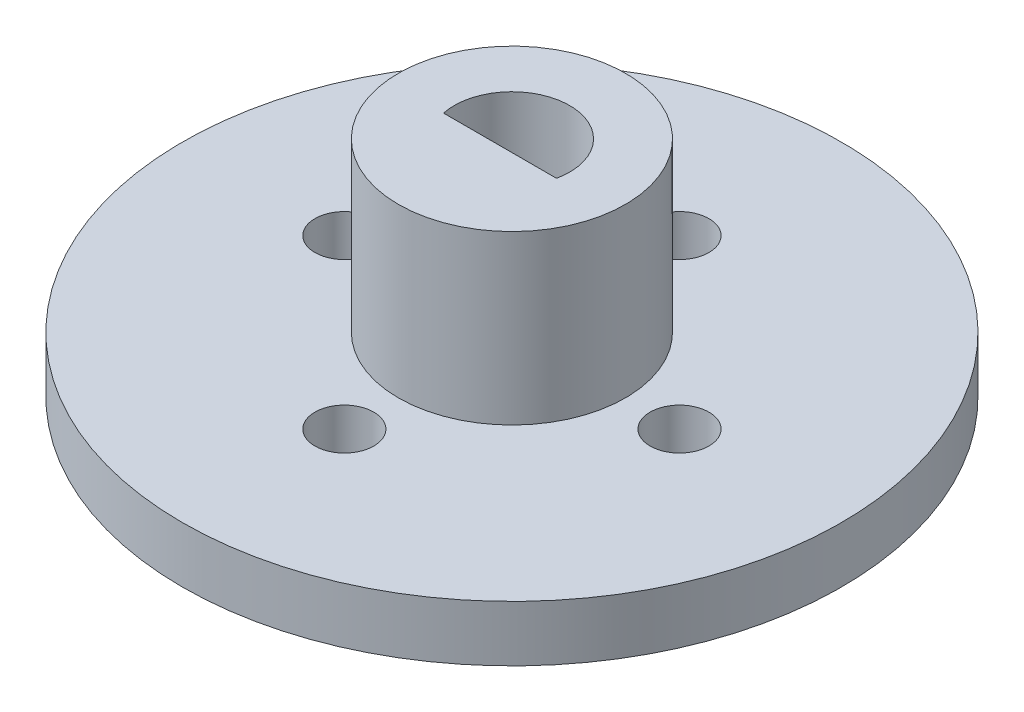
SolidWorks part; units mm, degrees
ref_plane "Front Plane" through (0, 0, 0) normal (0, 0, 1) x (1, 0, 0)
ref_plane "Top Plane" through (0, 0, 0) normal (0, 1, 0) x (1, 0, 0)
ref_plane "Right Plane" through (0, 0, 0) normal (1, 0, 0) x (0, 0, -1)
sketch "Sketch2" plane through (0, 0, 0) normal (0, 1, 0) x (-1, 0, 0)
  circle A0 centre (0, 0) radius 17.7
  dimension "D1" = 35.4
extrude "Boss-Extrude3" add sketch "Sketch2" along normal blind 3
sketch "Sketch3" plane through (0, 0, 0) normal (0, 1, 0) x (1, 0, 0)
  circle A0 centre (0, 0) radius 3.1
  dimension "D1" = 6.2
extrude "Cut-Extrude3" cut sketch "Sketch3" against normal through all and the other way through all
sketch "Sketch5" plane through (0, 3, 0) normal (0, 1, 0) x (1, 0, 0)
  circle A0 centre (0, 0) radius 6.1
  circle A1 centre (0, 0) radius 3.1 construction
  dimension "D1" = 3
extrude "Boss-Extrude4" add sketch "Sketch5" along normal blind 9
sketch "Sketch4" plane through (0, 0, 0) normal (0, 1, 0) x (1, 0, 0)
  line L0 (0, -6.6) -> (0, 6.6) construction
  line L1 (-6.6, 0) -> (6.6, 0) construction
  circle A0 centre (-9, 0) radius 1.58
  circle A3 centre (0, 0) radius 3.1 construction
  circle A4 centre (9, 0) radius 1.58
  circle A6 centre (0, 9) radius 1.58
  circle A7 centre (0, 0) radius 6.1 construction
  circle A8 centre (0, -9) radius 1.58
  dimension "D1" = 3.16
  dimension "D2" = 3.16
  dimension "D3" = 9
  dimension "D4" = 9
extrude "Cut-Extrude4" cut sketch "Sketch4" along normal through all both and the other way through all
sketch "Sketch6" plane through (0, 3, 0) normal (0, -1, 0) x (1, 0, 0)
  circle A0 centre (0, 0) radius 3.1
  circle A1 centre (0, 0) radius 3.1 construction
extrude "Cut-Extrude5" cut sketch "Sketch6" against normal blind 10
sketch "Sketch7" plane through (0, 0, 0) normal (0, -1, 0) x (1, 0, 0)
  line L1 (-3.1, 3.1) -> (3.1, 3.1)
  line L2 (-3.1, 3.1) -> (-3.1, 0.64)
  line L3 (-3.1, 0.64) -> (3.1, 0.64)
  line L4 (3.1, 3.1) -> (3.1, 0.64)
  line L5 (-3.1, 3.1) -> (3.1, 0.64) construction
  line L6 (-3.1, 0.64) -> (3.1, 3.1) construction
  circle A0 centre (0, 0) radius 3.1 construction
  point P0 (0, 1.87)
  point P5 (0, 0)
  dimension "D1" = 0.64
extrude "Boss-Extrude5" add sketch "Sketch7" against normal up to surface (12 mm away) up to face at (0, 12, 3.1)
